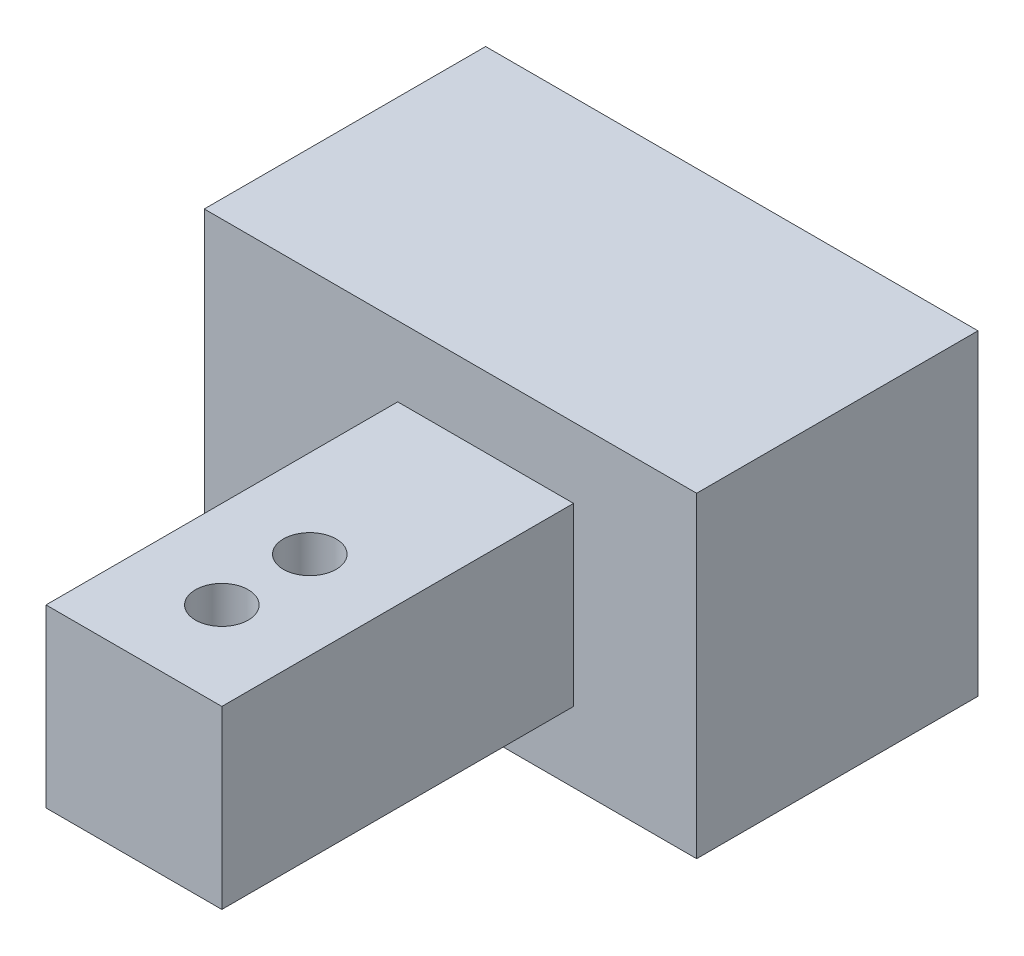
SolidWorks part; units mm, degrees
ref_plane "Front Plane" through (0, 0, 0) normal (0, 0, 1) x (1, 0, 0)
ref_plane "Top Plane" through (0, 0, 0) normal (0, 1, 0) x (1, 0, 0)
ref_plane "Right Plane" through (0, 0, 0) normal (1, 0, 0) x (0, 0, -1)
sketch "Sketch1" plane through (0, 0, 0) normal (0, 1, 0) x (1, 0, 0)
  line L1 (-13.5385, 5.3538) -> (14.4615, 5.3538)
  line L2 (-13.5385, 5.3538) -> (-13.5385, -10.6462)
  line L3 (-13.5385, -10.6462) -> (14.4615, -10.6462)
  line L4 (14.4615, 5.3538) -> (14.4615, -10.6462)
  dimension "D1" = 16
  dimension "D2" = 28
extrude "Boss-Extrude1" add sketch "Sketch1" along normal blind 18
sketch "Sketch3" plane through (0, 0, 10.6462) normal (0, 0, 1) x (1, 0, 0)
  line L0 (-13.5385, 18) -> (14.4615, 18) construction
  line L1 (-2.5385, 14) -> (7.4615, 14)
  line L2 (-2.5385, 14) -> (-2.5385, 4)
  line L3 (-2.5385, 4) -> (7.4615, 4)
  line L4 (7.4615, 14) -> (7.4615, 4)
  line L5 (-13.5385, 0) -> (14.4615, 0) construction
  line L6 (14.4615, 18) -> (14.4615, 0) construction
  point P8 (14.4615, 9)
  dimension "D1" = 10
  dimension "D2" = 10
  dimension "D3" = 4
  dimension "D4" = 14
  dimension "D5" = 7
extrude "Boss-Extrude3" add sketch "Sketch3" along normal blind 20
sketch "Sketch4" plane through (0, 14, 0) normal (0, 1, 0) x (1, 0, 0)
  line L0 (7.4615, -10.6462) -> (-2.5385, -10.6462) construction
  line L1 (-2.5385, -30.6462) -> (-2.5385, -10.6462) construction
  circle A0 centre (2.4615, -20.6462) radius 1.5
  circle A1 centre (2.4615, -25.6462) radius 1.5
  dimension "D1" = 3
  dimension "D2" = 5
  dimension "D4" = 5
  dimension "D5" = 5
  dimension "D3" = 10
extrude "Cut-Extrude1" cut sketch "Sketch4" against normal blind 20
sketch "Sketch5" plane through (-13.5385, 0, 0) normal (-1, 0, 0) x (0, 0, 1)
  line L0 (-5.3538, 18) -> (10.6462, 18) construction
  line L1 (-3.3538, 16) -> (8.6462, 16)
  line L2 (-3.3538, 16) -> (-3.3538, 2)
  line L3 (-3.3538, 2) -> (8.6462, 2)
  line L4 (8.6462, 16) -> (8.6462, 2)
  line L5 (-5.3538, 18) -> (-5.3538, 0) construction
  line L6 (10.6462, 14) -> (10.6462, 4) construction
  line L7 (-5.3538, 0) -> (10.6462, 0) construction
  dimension "D1" = 2
  dimension "D2" = 2
  dimension "D3" = 2
  dimension "D4" = 2
extrude "Cut-Extrude2" cut sketch "Sketch5" against normal blind 26
